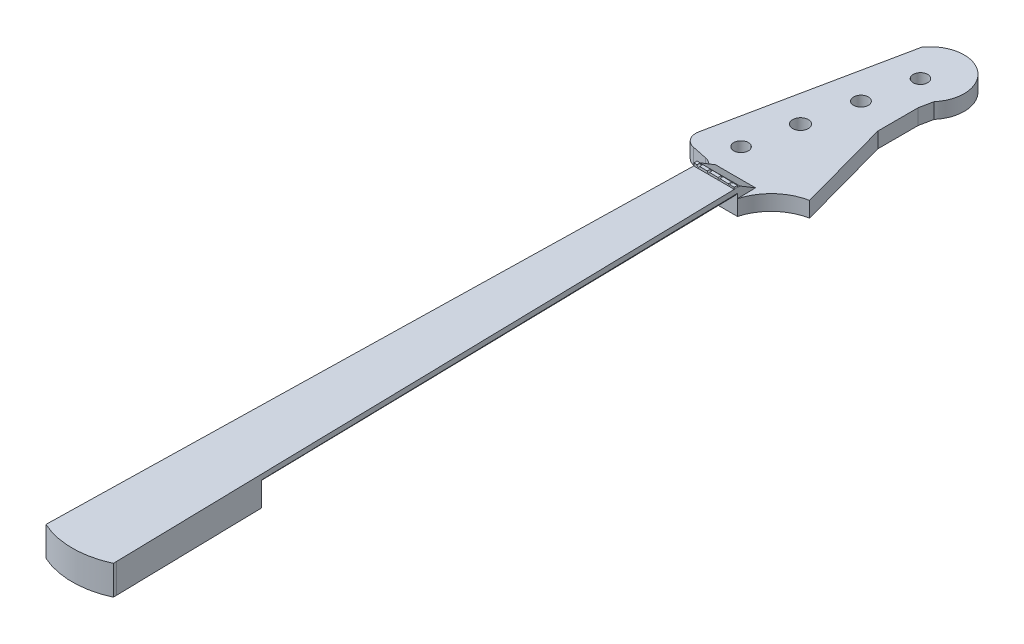
SolidWorks part; units mm, degrees
ref_plane "Front Plane" through (0, 0, 0) normal (0, 0, 1) x (1, 0, 0)
ref_plane "Top Plane" through (0, 0, 0) normal (0, 1, 0) x (1, 0, 0)
ref_plane "Right Plane" through (0, 0, 0) normal (1, 0, 0) x (0, 0, -1)
sketch "Sketch1" plane through (0, 0, 0) normal (0, 0, 1) x (1, 0, 0)
  line L0 (-19.05, 0) -> (19.05, 0)
  line L1 (19.05, 0) -> (19.05, -4.826)
  line L2 (19.05, -4.826) -> (-19.05, -4.826)
  line L3 (-19.05, -4.826) -> (-19.05, 0)
  point P6 (0, 0)
  dimension "D1" = 38.1
  dimension "D2" = 4.826
ref_plane "Plane1" through (0, 0, 598.4875) normal (0, 0, 1) x (1, 0, 0)
sketch "Sketch2" plane through (0, 0, 598.4875) normal (0, 0, 1) x (1, 0, 0)
  line L0 (19.05, -4.826) -> (-19.05, -4.826) construction
  line L1 (-31.75, 0) -> (31.75, 0)
  line L2 (-31.75, 0) -> (-31.75, -4.826)
  line L3 (-31.75, -4.826) -> (31.75, -4.826)
  line L4 (31.75, 0) -> (31.75, -4.826)
  line L5 (-19.05, 0) -> (19.05, 0) construction
  point P8 (0, 0)
  dimension "D1" = 63.5
loft "Loft1" add profiles "Sketch1", "Sketch2"
sketch "Sketch3" plane through (0, 0, 0) normal (0, 0, -1) x (-1, 0, 0)
  line L0 (19.05, -4.826) -> (-19.05, -4.826) construction
  line L1 (19.05, -4.826) -> (-19.05, -4.826)
  arc A0 (-19.05, -4.826) -> (19.05, -4.826) centre (0, 7.5791) ccw
  dimension "D1" = 22.733
ref_plane "Plane2" through (0, 0, 458.7875) normal (0, 0, 1) x (1, 0, 0)
sketch "Sketch5" plane through (0, -4.826, 0) normal (0, -1, 0) x (1, 0, 0)
  line L0 (19.05, 0) -> (31.75, 598.4875) construction
  line L1 (28.7855, 458.7875) -> (31.75, 598.4875)
  line L2 (-19.05, 0) -> (-31.75, 598.4875) construction
  line L3 (-28.7855, 458.7875) -> (-31.75, 598.4875)
  line L4 (-31.75, 598.4875) -> (31.75, 598.4875)
  line L5 (-28.7855, 458.7875) -> (28.7855, 458.7875)
  line L6 (13.6811, 458.7875) -> (-13.6811, 458.7875) construction
extrude "Boss-Extrude1" add sketch "Sketch5" along normal blind 22.86
sketch "Sketch4" plane through (0, 0, 458.7875) normal (0, 0, 1) x (1, 0, 0)
  line L3 (-28.7855, -4.826) -> (28.7855, -4.826)
  line L4 (-19.05, -4.826) -> (19.05, -4.826) construction
  line L5 (-28.7855, -4.826) -> (28.7855, -4.826) construction
  arc A1 (-28.7855, -4.826) -> (28.7855, -4.826) centre (0, 18.034) ccw
  point P6 (0, -4.826)
  point P9 (0, -4.826)
  dimension "D1" = 22.86
loft "Loft2" add profiles "Sketch4", "Sketch3"
sketch "Sketch6" plane through (0, 0, 0) normal (0, 1, 0) x (1, 0, 0)
  line L0 (-31.75, -598.4875) -> (-31.75, -601.5355)
  line L2 (31.75, -598.4875) -> (31.75, -601.5355)
  line L5 (31.75, -598.4875) -> (-31.75, -598.4875) construction
  line L6 (31.75, -598.4875) -> (-31.75, -598.4875)
  arc A0 (-31.75, -601.5355) -> (31.75, -601.5355) centre (0, -532.8689) ccw
  point P2 (0, -608.5205)
  dimension "D1" = 6.985
  dimension "D2" = 3.048
extrude "Boss-Extrude2" add sketch "Sketch6" against normal up to surface (27.686 mm away) up to face at (0, -27.686, 528.6375)
ref_plane "Plane3" through (0, -23.749, 0) normal (0, 1, 0) x (1, 0, 0)
sketch "Sketch7" plane through (0, -23.749, 0) normal (0, 1, 0) x (1, 0, 0)
  line L0 (-53.7966, 36.3949) -> (-17.8583, 210.525)
  line L1 (-43.9257, 21.39) -> (-29.183, 18.3473)
  line L2 (32.5646, 172.0943) -> (29.9976, 159.6564)
  line L3 (-19.05, 0) -> (19.05, 0)
  line L4 (19.05, 0) -> (19.1268, -3.6195) construction
  line L5 (19.05, 0) -> (31.75, -598.4875) construction
  line L6 (19.1268, -3.6195) -> (-19.1268, -3.6195) construction
  line L7 (-19.05, 0) -> (-31.75, -598.4875) construction
  line L8 (-19.1268, -3.6195) -> (-19.05, 0) construction
  line L9 (-14.859, 0) -> (-14.859, -3.6195) construction
  line L10 (-4.7244, 0) -> (-4.7244, -3.6195) construction
  line L11 (4.572, 0) -> (4.572, -3.6195) construction
  line L12 (14.097, 0) -> (14.097, -3.6195) construction
  line L13 (-14.859, 0) -> (-14.859, 44.196) construction
  line L14 (-4.7244, 0) -> (-4.7244, 90.7136) construction
  line L15 (4.572, 0) -> (4.572, 137.9775) construction
  line L16 (14.097, 0) -> (14.097, 184.4951) construction
  line L17 (-21.7234, 44.196) -> (7.2326, 184.4951) construction
  line L18 (-19.05, 5.9095) -> (-19.05, 0)
  line L19 (29.9976, 159.6564) -> (29.9976, 121.5564)
  line L20 (29.9976, 121.5564) -> (54.4767, 32.6564)
  arc A1 (32.5646, 172.0943) -> (-17.8583, 210.525) centre (8.4403, 192.7361) ccw
  circle A2 centre (-21.7234, 44.196) radius 6.8643
  circle A3 centre (-12.1227, 90.7136) radius 7.3983
  circle A4 centre (-2.368, 137.9775) radius 6.94
  circle A5 centre (7.2326, 184.4951) radius 6.8643
  arc A7 (19.05, 0) -> (54.4767, 32.6564) centre (63.1003, -12.2429) cw
  arc A8 (-29.183, 18.3473) -> (-19.05, 5.9095) centre (-31.75, 5.9095) cw
  arc A9 (-53.7966, 36.3949) -> (-43.9257, 21.39) centre (-41.3587, 33.8279) ccw
  point P45 (-19.05, 16.256)
  point P48 (-56.3636, 23.9571)
  dimension "D4" = 13.7287
  dimension "D14" = 14.7966
  dimension "D16" = 63.5
  dimension "D19" = 45.72
  dimension "D20" = 12.7
  dimension "D1" = 190.5
  dimension "D2" = 38.1
  dimension "D3" = 57.15
  dimension "D5" = 3.6195
  dimension "D6" = 4.191
  dimension "D7" = 10.1346
  dimension "D8" = 19.431
  dimension "D9" = 28.956
  dimension "D10" = 47.498
  dimension "D11" = 95.758
  dimension "D12" = 143.256
  dimension "D13" = 44.196
  dimension "D15" = 16.256
  dimension "D17" = 12.7
  dimension "D18" = 76.2
  dimension "D21" = 88.9
  dimension "D22" = 38.1
  dimension "D23" = 172.0943
  dimension "D24" = 164.605
extrude "Boss-Extrude3" add sketch "Sketch7" along normal blind 14.5542
sketch "Sketch8" plane through (-19.05, 0, 0) normal (-1, 0, 0) x (0, 0, 1)
  line L0 (0, 0) -> (-2.286, 0)
  line L1 (-2.286, 0) -> (-17.399, -9.1948)
  line L3 (-5.9095, -9.1948) -> (-18.3473, -9.1948) construction
  line L4 (-17.399, -9.1948) -> (0, -9.1948)
  line L5 (0, -9.1948) -> (0, 0)
  dimension "D1" = 2.286
  dimension "D2" = 17.399
extrude "Boss-Extrude4" add sketch "Sketch8" against normal up to surface (37.7308 mm away)
sketch "Sketch9" plane through (0, -27.686, 0) normal (0, -1, 0) x (1, 0, 0)
  line L0 (28.7855, 458.7875) -> (31.75, 598.4875) construction
  line L1 (18.9681, 572.2902) -> (18.9681, 606.104) construction
  line L2 (-31.75, 598.4875) -> (-28.7855, 458.7875) construction
  circle A0 centre (-18.4599, 572.2902) radius 2.0637
  circle A1 centre (18.9681, 572.2902) radius 2.0637
  circle A2 centre (19.0266, 521.1727) radius 2.0637
  circle A3 centre (-18.1374, 521.1727) radius 2.0637
  arc A4 (31.75, 601.5355) -> (-31.75, 601.5355) centre (0, 532.8689) ccw construction
  point P8 (21.0318, 572.2902)
  point P11 (18.9681, 570.2265)
  point P12 (19.0266, 523.2365)
  point P13 (21.0903, 521.1727)
  point P14 (18.9681, 574.354)
  point P20 (-20.5237, 572.2902)
  point P22 (-20.2011, 521.1727)
  dimension "D1" = 4.1275
  dimension "D2" = 10.16
  dimension "D3" = 46.99
  dimension "D4" = 9.017
  dimension "D5" = 31.75
  dimension "D6" = 10.668
  dimension "D7" = 9.906
extrude "Cut-Extrude1" cut sketch "Sketch9" against normal blind 10.16
sketch "Sketch10" plane through (0, 0, 0) normal (0, 0, 1) x (1, 0, 0)
  line L0 (-19.05, 0) -> (19.0015, 0)
  line L1 (18.6808, -9.1948) -> (19.0015, 0) construction
  line L2 (19.0015, 0) -> (-19.05, 0) construction
  line L3 (19.0015, 0) -> (19.0015, 1.6637)
  line L4 (19.0015, 1.6637) -> (14.9098, 1.7579)
  line L5 (-19.05, 2.54) -> (-19.05, 0)
  line L6 (13.6906, 1.786) -> (5.5057, 1.9745)
  line L7 (3.8039, 2.0137) -> (-4.2838, 2.1999)
  line L8 (-6.3534, 2.2476) -> (-13.5382, 2.4131)
  line L9 (-16.0782, 2.4716) -> (-19.05, 2.54)
  arc A0 (-13.5382, 2.4131) -> (-16.0782, 2.4716) centre (-14.8082, 2.4423) cw
  arc A1 (-4.2838, 2.1999) -> (-6.3534, 2.2476) centre (-5.3186, 2.2238) cw
  arc A2 (5.5057, 1.9745) -> (3.8039, 2.0137) centre (4.6548, 1.9941) cw
  arc A3 (14.9098, 1.7579) -> (13.6906, 1.786) centre (14.3002, 1.772) cw
  point P22 (-15.414, 4.699)
  point P23 (-15.5104, 2.4878)
  point P24 (0, 0)
  point P25 (0, 0)
  point P26 (0, 0)
  dimension "D1" = 2.54
  dimension "D2" = 1.6637
  dimension "D3" = 2.54
  dimension "D4" = 2.9718
  dimension "D5" = 2.0701
  dimension "D6" = 12.7
  dimension "D7" = 1.7018
  dimension "D8" = 22.86
  dimension "D9" = 1.2192
  dimension "D10" = 32.7406
extrude "Boss-Extrude5" add sketch "Sketch10" along normal blind 3.048
sketch "Sketch11" plane through (0, 0, 0) normal (0, 1, 0) x (1, 0, 0)
  line L0 (-19.05, 0) -> (-31.75, -598.4875) construction
  line L1 (19.0015, 2.286) -> (31.75, -598.4875) construction
  line L2 (-19.05, 0) -> (-31.75, -598.4875) construction
  line L3 (19.0015, 2.286) -> (31.75, -598.4875) construction
  line L4 (-20.1253, -50.673) -> (20.1253, -50.673) construction
  line L5 (13.6906, -3.048) -> (5.5057, -3.048) construction
  line L6 (-21.1022, -96.7105) -> (21.1022, -96.7105) construction
  line L7 (-19.05, -3.048) -> (19.0015, -3.048) construction
  line L8 (-22.0118, -139.573) -> (22.0118, -139.573) construction
  line L9 (-22.8876, -180.848) -> (22.8876, -180.848) construction
  line L10 (-23.6961, -218.948) -> (23.6961, -218.948) construction
  line L11 (-24.4709, -255.4605) -> (24.4709, -255.4605) construction
  line L12 (-25.1783, -288.798) -> (25.1783, -288.798) construction
  line L13 (-25.8858, -322.1355) -> (25.8858, -322.1355) construction
  line L14 (3.8039, -3.048) -> (-4.2838, -3.048) construction
  line L15 (-26.5258, -352.298) -> (26.5258, -352.298) construction
  line L16 (-27.1322, -380.873) -> (27.1322, -380.873) construction
  line L17 (-27.7049, -407.8605) -> (27.7049, -407.8605) construction
  line L18 (-28.2775, -434.848) -> (28.2775, -434.848) construction
  line L19 (-28.7492, -457.073) -> (28.7492, -457.073) construction
  line L20 (-29.2545, -480.8855) -> (29.2545, -480.8855) construction
  line L21 (-29.7261, -503.1105) -> (29.7261, -503.1105) construction
  line L22 (-30.164, -523.748) -> (30.164, -523.748) construction
  line L23 (-30.5683, -542.798) -> (30.5683, -542.798) construction
  line L24 (-31.3094, -577.723) -> (31.3094, -577.723) construction
  line L25 (-31.6462, -593.598) -> (31.6462, -593.598) construction
  line L26 (-30.9388, -560.2605) -> (30.9388, -560.2605) construction
  dimension "D1" = 47.625
  dimension "D2" = 93.6625
  dimension "D3" = 136.525
  dimension "D4" = 177.8
  dimension "D5" = 215.9
  dimension "D6" = 252.4125
  dimension "D7" = 285.75
  dimension "D8" = 319.0875
  dimension "D9" = 349.25
  dimension "D10" = 377.825
  dimension "D11" = 404.8125
  dimension "D12" = 431.8
  dimension "D13" = 454.025
  dimension "D14" = 477.8375
  dimension "D15" = 500.0625
  dimension "D16" = 520.7
  dimension "D17" = 539.75
  dimension "D18" = 574.675
  dimension "D19" = 590.55
  dimension "D20" = 557.2125
